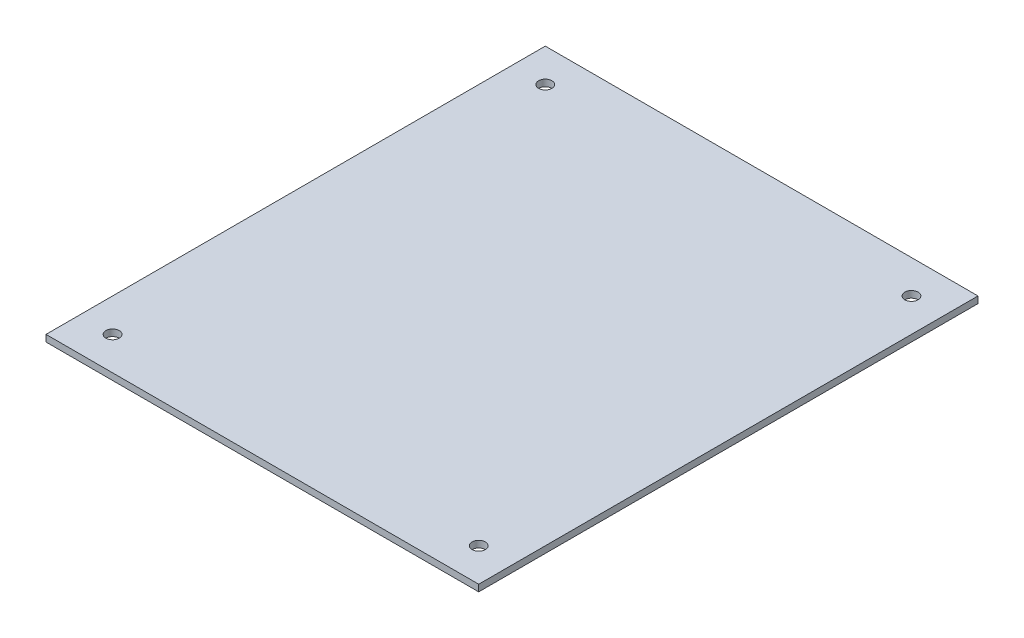
SolidWorks part; units mm, degrees
ref_plane "Front Plane" through (0, 0, 0) normal (0, 0, 1) x (1, 0, 0)
ref_plane "Top Plane" through (0, 0, 0) normal (0, 1, 0) x (1, 0, 0)
ref_plane "Right Plane" through (0, 0, 0) normal (1, 0, 0) x (0, 0, -1)
sketch "Sketch1" plane through (0, 0, 0) normal (0, 1, 0) x (1, 0, 0)
  line L1 (-65, -75) -> (65, -75)
  line L2 (-65, -75) -> (-65, 75)
  line L3 (-65, 75) -> (65, 75)
  line L4 (65, -75) -> (65, 75)
  line L5 (-65, -75) -> (65, 75) construction
  line L6 (-65, 75) -> (65, -75) construction
  point P0 (0, 0)
  dimension "D1" = 130
  dimension "D2" = 150
extrude "Boss-Extrude1" add sketch "Sketch1" along normal blind 2
sketch "Sketch2" plane through (0, 2, 0) normal (0, 1, 0) x (1, 0, 0)
  line L0 (0, 0) -> (0, 50000) construction
  line L1 (0, 0) -> (50000, 0) construction
  line L2 (65, 75) -> (-65, 75) construction
  line L3 (-65, 75) -> (-65, -75) construction
  circle A0 centre (-55, 65) radius 2
  circle A1 centre (55, 65) radius 2
  circle A2 centre (55, -65) radius 2
  circle A3 centre (-55, -65) radius 2
  dimension "D1" = 10
  dimension "D2" = 10
  dimension "D3" = 4
extrude "Cut-Extrude1" cut sketch "Sketch2" against normal through all
